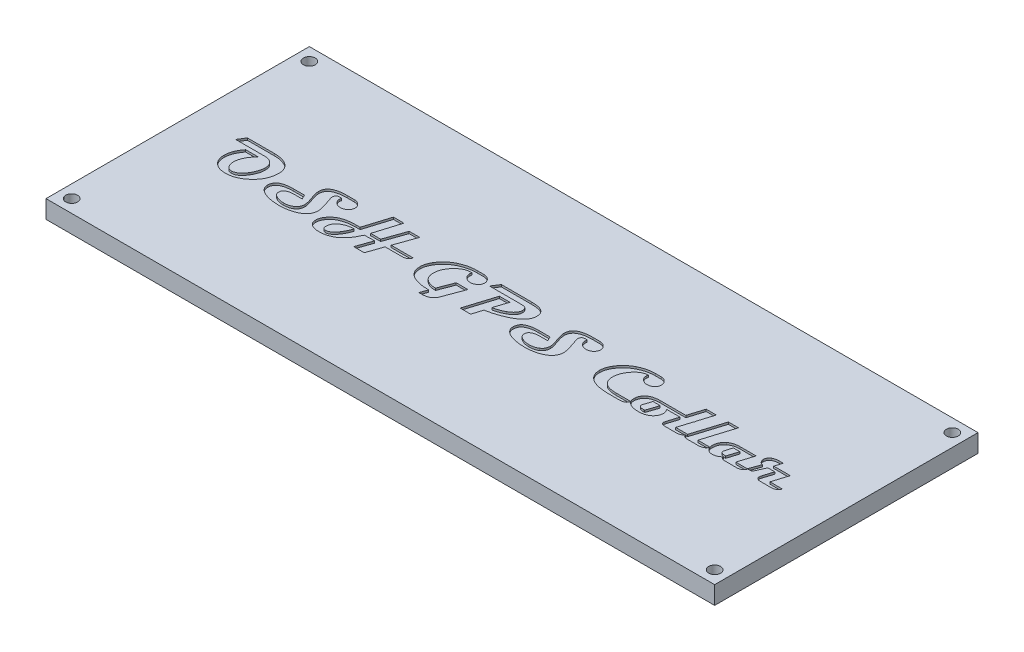
SolidWorks part; units mm, degrees
ref_plane "Front Plane" through (0, 0, 0) normal (0, 0, 1) x (1, 0, 0)
ref_plane "Top Plane" through (0, 0, 0) normal (0, 1, 0) x (1, 0, 0)
ref_plane "Right Plane" through (0, 0, 0) normal (1, 0, 0) x (0, 0, -1)
sketch "Sketch1" plane through (0, 0, 0) normal (0, 1, 0) x (1, 0, 0)
  line L1 (0, 0) -> (165.1, 0)
  line L2 (0, 0) -> (0, 65.024)
  line L3 (0, 65.024) -> (165.1, 65.024)
  line L4 (165.1, 0) -> (165.1, 65.024)
  circle A0 centre (3.175, 61.849) radius 1.4605
  circle A1 centre (3.175, 3.175) radius 1.4605
  circle A2 centre (161.925, 3.175) radius 1.4605
  circle A3 centre (161.925, 61.849) radius 1.4605
  dimension "D3" = 2.921
  dimension "D8" = 2.921
  dimension "D11" = 2.921
  dimension "D12" = 2.921
  dimension "D1" = 165.1
  dimension "D2" = 65.024
  dimension "D4" = 3.175
  dimension "D5" = 3.175
  dimension "D6" = 3.175
  dimension "D7" = 3.175
  dimension "D9" = 3.175
  dimension "D10" = 3.175
  dimension "D13" = 3.175
  dimension "D14" = 3.175
extrude "Boss-Extrude1" add sketch "Sketch1" along normal blind 4.445
sketch "Sketch2" plane through (0, 4.445, 0) normal (0, 1, 0) x (1, 0, 0)
  text T0 "OSH GPS Collar" font "Magneto" height in points 36
extrude "Cut-Extrude1" cut sketch "Sketch2" against normal blind 0.508
